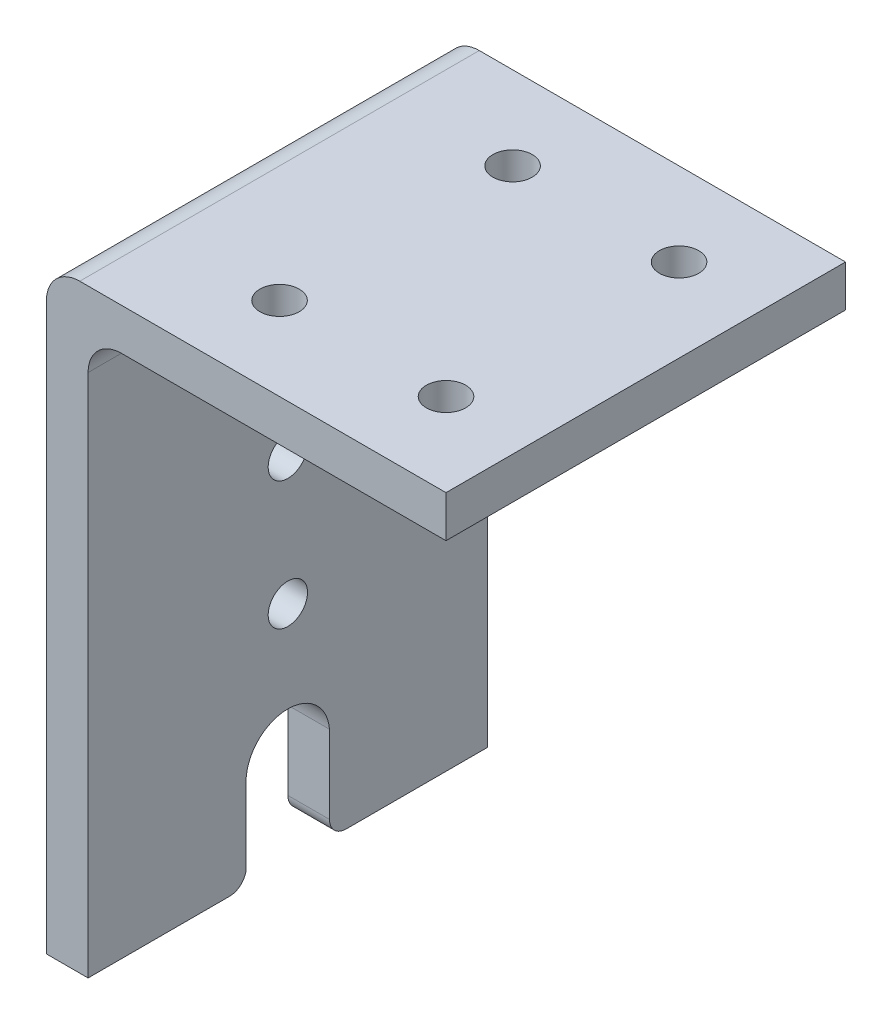
SolidWorks part; units mm, degrees
material "PET"
ref_plane "Front Plane" through (0, 0, 0) normal (0, 0, 1) x (1, 0, 0)
ref_plane "Top Plane" through (0, 0, 0) normal (0, 1, 0) x (1, 0, 0)
ref_plane "Right Plane" through (0, 0, 0) normal (1, 0, 0) x (0, 0, -1)
sketch "Sketch1" plane through (0, 0, 0) normal (0, 0, 1) x (1, 0, 0)
  line L0 (-1.5875, 3.175) -> (-1.5875, -42.545)
  line L5 (-1.5875, -42.545) -> (1.5875, -42.545)
  line L6 (1.5875, -42.545) -> (1.5875, 0)
  line L7 (-1.5875, 3.175) -> (28.8925, 3.175)
  line L8 (28.8925, 3.175) -> (28.8925, 0)
  line L9 (28.8925, 0) -> (1.5875, 0)
  line L10 (0, 3.175) -> (0, -42.545) construction
  line L11 (28.8925, 1.5875) -> (-1.5875, 1.5875) construction
  point P0 (0, 0)
  dimension "D1" = 3.175
  dimension "D2" = 45.72
  dimension "D3" = 30.48
extrude "Boss-Extrude1" add sketch "Sketch1" along normal blind 30.48
fillet "Fillet1" radius 2.54 2 edges at (1.5875, 0, 15.24) (-1.5875, 3.175, 15.24)
sketch "Sketch2" plane through (1.5875, 0, 0) normal (1, 0, 0) x (0, 0, -1)
  line L0 (-15.24, -42.545) -> (-15.24, -2.54) construction
  line L1 (-30.48, -42.545) -> (0, -42.545) construction
  line L2 (0, -2.54) -> (-30.48, -2.54) construction
  point P10 (-15.24, -25.4381)
  point P13 (-15.24, -15.6591)
  dimension "D1" = 17.1069
  dimension "D6" = 9.779
hole_wizard "Ø3.0 (3) Diameter Hole2" positions "Sketch2" profile "Sketch3" hole size "Ø3.0" standard "ANSI Metric" end condition up to next
sketch "Sketch3" plane through (1.5875, -15.6591, 15.24) normal (0, 1, 0) x (0, 0, -1)
  line L0 (0, 0) -> (0, 3.175)
  line L1 (0, 3.175) -> (1.5, 3.175)
  line L2 (1.5, 3.175) -> (1.5, 0)
  line L5 (1.5, 0) -> (0, 0)
  line L11 (0, -6.35) -> (0, 107.95) construction
  dimension "Thru Hole Dia." = 3
  dimension "Thru Hole Depth" = 3.175
sketch "Sketch5" plane through (0, 0, 0) normal (0, -1, 0) x (-1, 0, 0)
  line L0 (-4.1275, 0) -> (-28.8925, 0) construction
  line L1 (-4.1275, -30.48) -> (-28.8925, -30.48) construction
  line L2 (-28.8925, -30.48) -> (-28.8925, 0) construction
  point P0 (-22.5425, -6.35)
  point P2 (-9.8425, -6.35)
  point P4 (-9.8425, -24.13)
  point P6 (-22.5425, -24.13)
  dimension "D1" = 6.35
  dimension "D2" = 6.35
  dimension "D3" = 6.35
  dimension "D4" = 6.35
  dimension "D5" = 12.7
  dimension "D6" = 12.7
  dimension "D7" = 6.35
  dimension "D8" = 6.35
hole_wizard "Ø3.0 (3) Diameter Hole1" positions "Sketch5" profile "Sketch6" hole size "Ø3.0" standard "ANSI Metric" end condition up to next
sketch "Sketch6" plane through (22.5425, 0, 6.35) normal (1, 0, 0) x (0, 0, -1)
  line L0 (0, 0) -> (0, 3.175)
  line L1 (0, 3.175) -> (1.5, 3.175)
  line L2 (1.5, 3.175) -> (1.5, 0)
  line L5 (1.5, 0) -> (0, 0)
  line L11 (0, -6.35) -> (0, 107.95) construction
  dimension "Thru Hole Dia." = 3
  dimension "Thru Hole Depth" = 3.175
sketch "Sketch7" plane through (1.5875, 0, 0) normal (1, 0, 0) x (0, 0, -1)
  line L0 (-15.24, -42.545) -> (-15.24, -35.57) construction
  line L1 (-30.48, -42.545) -> (0, -42.545) construction
  line L2 (-18.415, -42.545) -> (-18.415, -35.3175)
  line L3 (-12.065, -42.545) -> (-12.065, -35.3175)
  line L4 (-18.415, -42.545) -> (-12.065, -42.545)
  arc A1 (-12.065, -35.3175) -> (-18.415, -35.3175) centre (-15.24, -35.57) ccw
  point P0 (0, 0)
  point P4 (-15.24, -42.545)
  dimension "D3" = 3.185
  dimension "D1" = 10.16
  dimension "D2" = 6.35
extrude "Cut-Extrude1" cut sketch "Sketch7" against normal up to surface (3.175 mm away) up to face at (-1.5875, -23.9381, 15.24)
fillet "Fillet2" radius 1.27 2 edges at (0, -42.545, 12.065) (0, -42.545, 18.415)
